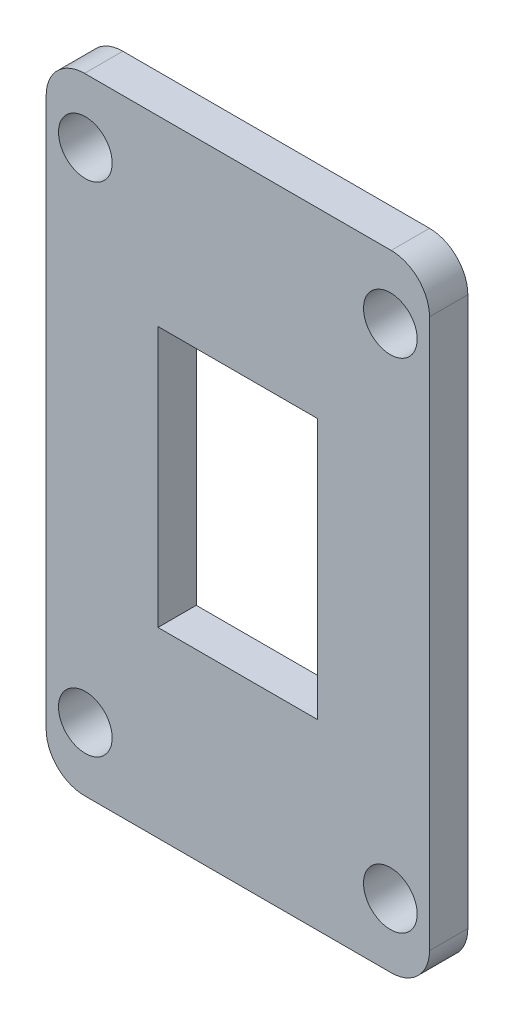
SolidWorks part; units mm, degrees
ref_plane "Front Plane" through (0, 0, 0) normal (0, 0, 1) x (1, 0, 0)
ref_plane "Top Plane" through (0, 0, 0) normal (0, 1, 0) x (1, 0, 0)
ref_plane "Right Plane" through (0, 0, 0) normal (1, 0, 0) x (0, 0, -1)
sketch "Sketch1" plane through (0, 0, 0) normal (0, 0, 1) x (1, 0, 0)
  line L1 (-15, 24.48) -> (15, 24.48)
  line L2 (-15, 24.48) -> (-15, -24.48)
  line L3 (-15, -24.48) -> (15, -24.48)
  line L4 (15, 24.48) -> (15, -24.48)
  line L5 (-15, 24.48) -> (15, -24.48) construction
  line L6 (-15, -24.48) -> (15, 24.48) construction
  line L7 (-6.25, 10.2) -> (6.25, 10.2)
  line L8 (-6.25, 10.2) -> (-6.25, -10.2)
  line L9 (-6.25, -10.2) -> (6.25, -10.2)
  line L10 (6.25, 10.2) -> (6.25, -10.2)
  line L11 (-6.25, 10.2) -> (6.25, -10.2) construction
  line L12 (-6.25, -10.2) -> (6.25, 10.2) construction
  line L13 (-11.9363, 19.48) -> (11.9363, 19.48) construction
  line L14 (-11.9363, 19.48) -> (-11.9363, -19.48) construction
  line L15 (-11.9363, -19.48) -> (11.9363, -19.48) construction
  line L16 (11.9363, 19.48) -> (11.9363, -19.48) construction
  circle A0 centre (-11.9363, 19.48) radius 2.1
  circle A1 centre (11.9363, 19.48) radius 2.1
  circle A2 centre (11.9363, -19.48) radius 2.1
  circle A3 centre (-11.9363, -19.48) radius 2.1
  point P0 (0, 0)
  point P5 (0, 0)
  dimension "D4" = 5
  dimension "D5" = 4.2
  dimension "D6" = 4.2
  dimension "D7" = 4.2
  dimension "D8" = 4.2
  dimension "D1" = 20.4
  dimension "D2" = 12.5
  dimension "D3" = 30
extrude "Boss-Extrude1" add sketch "Sketch1" along normal blind 3
fillet "Fillet1" radius 3 4 edges at (-15, 24.48, 1.5) (-15, -24.48, 1.5) (15, -24.48, 1.5) (15, 24.48, 1.5)
